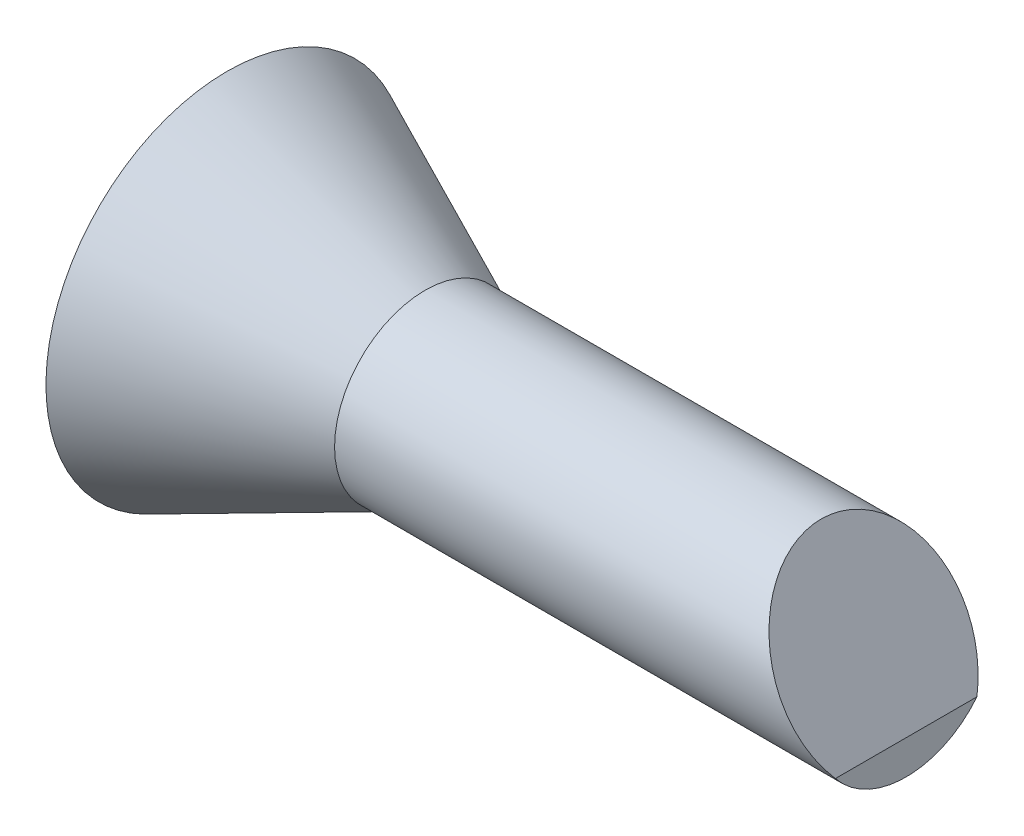
SolidWorks part; units mm, degrees
ref_plane "Front Plane" through (0, 0, 0) normal (0, 0, 1) x (1, 0, 0)
ref_plane "Top Plane" through (0, 0, 0) normal (0, 1, 0) x (1, 0, 0)
ref_plane "Right Plane" through (0, 0, 0) normal (1, 0, 0) x (0, 0, -1)
sketch "Sketch1" plane through (0, 0, 0) normal (0, 0, 1) x (1, 0, 0)
  line L0 (0, 0) -> (35, 16)
  line L1 (35, 16) -> (120, 16)
  line L2 (120, 16) -> (120, 32)
  line L3 (120, 32) -> (0, 32)
  line L4 (0, 32) -> (0, 0)
  dimension "D1" = 35
  dimension "D2" = 85
  dimension "D3" = 32
  dimension "D4" = 16
revolve "Revolve1" add sketch "Sketch1" angle 360 about L3
sketch "Sketch2" plane through (0, 0, 0) normal (0, 0, 1) x (1, 0, 0)
  line L0 (105, 48) -> (120, 22.0192)
  line L1 (120, 48) -> (35, 48) construction
  line L2 (120, 16) -> (120, 48) construction
  line L3 (120, 22.0192) -> (120, 48)
  line L4 (120, 48) -> (105, 48)
  line L5 (35, 16) -> (120, 16) construction
  dimension "D1" = 15
  dimension "D2" = 60
extrude "Cut-Extrude1" cut sketch "Sketch2" against normal mid plane 60
